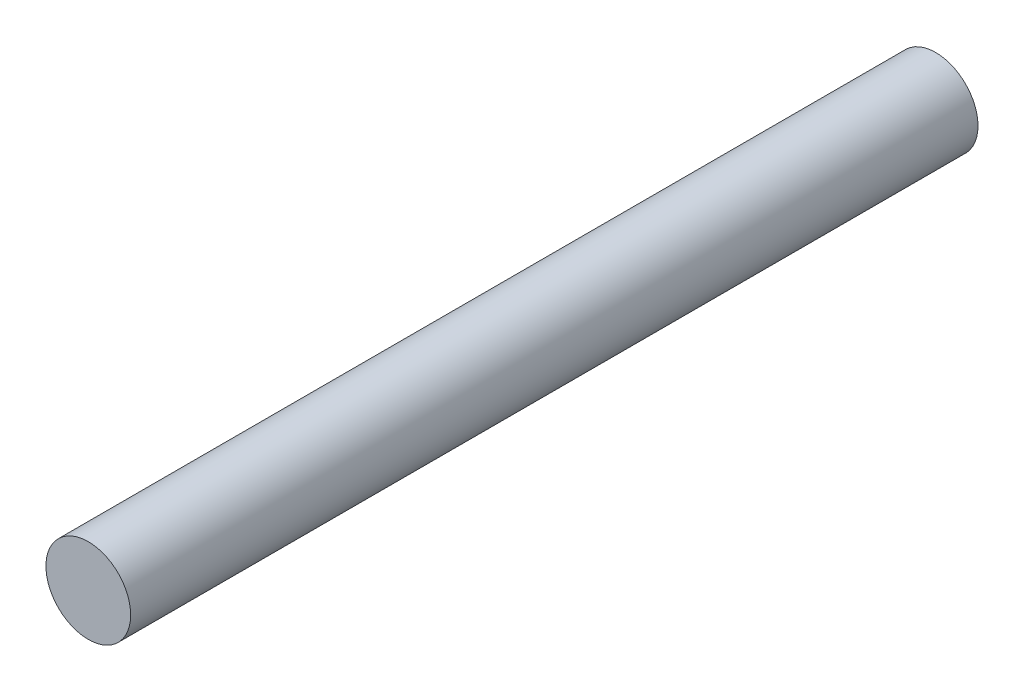
SolidWorks part; units mm, degrees
ref_plane "前视基准面" through (0, 0, 0) normal (0, 0, 1) x (1, 0, 0)
ref_plane "上视基准面" through (0, 0, 0) normal (0, 1, 0) x (1, 0, 0)
ref_plane "右视基准面" through (0, 0, 0) normal (1, 0, 0) x (0, 0, -1)
sketch "草图1" plane through (0, 0, 0) normal (0, 0, 1) x (1, 0, 0)
  circle A0 centre (0, 0) radius 2.5
  dimension "D1" = 5
extrude "凸台-拉伸1" add sketch "草图1" along normal blind 50
